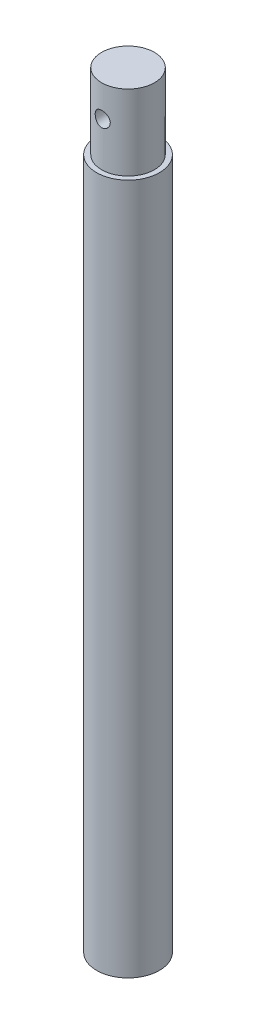
SolidWorks part; units mm, degrees
ref_plane "Front Plane" through (0, 0, 0) normal (0, 0, 1) x (1, 0, 0)
ref_plane "Top Plane" through (0, 0, 0) normal (0, 1, 0) x (1, 0, 0)
ref_plane "Right Plane" through (0, 0, 0) normal (1, 0, 0) x (0, 0, -1)
sketch "Sketch2" plane through (0, 0, 0) normal (0, 0, 1) x (1, 0, 0)
  line L0 (0, 0) -> (0, 57.2523) construction
  line L1 (0, 0) -> (12.5, 0)
  line L2 (12.5, 0) -> (12.5, 275)
  line L3 (12.5, 275) -> (10.5, 275)
  line L4 (10.5, 275) -> (10.5, 305)
  line L5 (10.5, 305) -> (0, 305)
  line L6 (0, 0) -> (0, 305)
  dimension "D1" = 25
  dimension "D2" = 275
  dimension "D3" = 30
  dimension "D4" = 21
revolve "Revolve1" add sketch "Sketch2" angle 360 about L0
sketch "Sketch3" plane through (0, 0, 0) normal (0, 0, 1) x (1, 0, 0)
  line L1 (0, -13.75) -> (0, 13.75) construction
  line L2 (10.5, 305) -> (-10.5, 305) construction
  circle A0 centre (0, 292.5) radius 3
  point P4 (0, 0)
  dimension "D2" = 6
  dimension "D1" = 12.5
extrude "Cut-Extrude1" cut sketch "Sketch3" against normal mid plane 50
